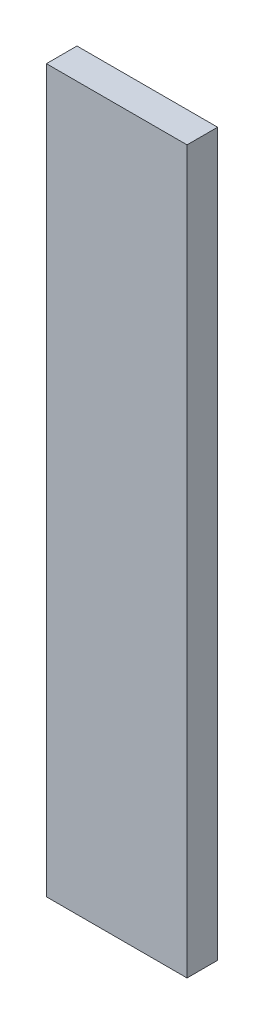
SolidWorks part; units mm, degrees
ref_plane "Front Plane" through (0, 0, 0) normal (0, 0, 1) x (1, 0, 0)
ref_plane "Top Plane" through (0, 0, 0) normal (0, 1, 0) x (1, 0, 0)
ref_plane "Right Plane" through (0, 0, 0) normal (1, 0, 0) x (0, 0, -1)
sketch "Sketch1" plane through (0, 0, 0) normal (0, 0, 1) x (1, 0, 0)
  line L0 (0, 46) -> (0, -190)
  line L3 (0, 46) -> (46, 46)
  line L4 (46, -190) -> (46, 46)
  line L5 (0, -190) -> (46, -190)
  dimension "D1" = 46
extrude "Boss-Extrude1" add sketch "Sketch1" along normal blind 10
